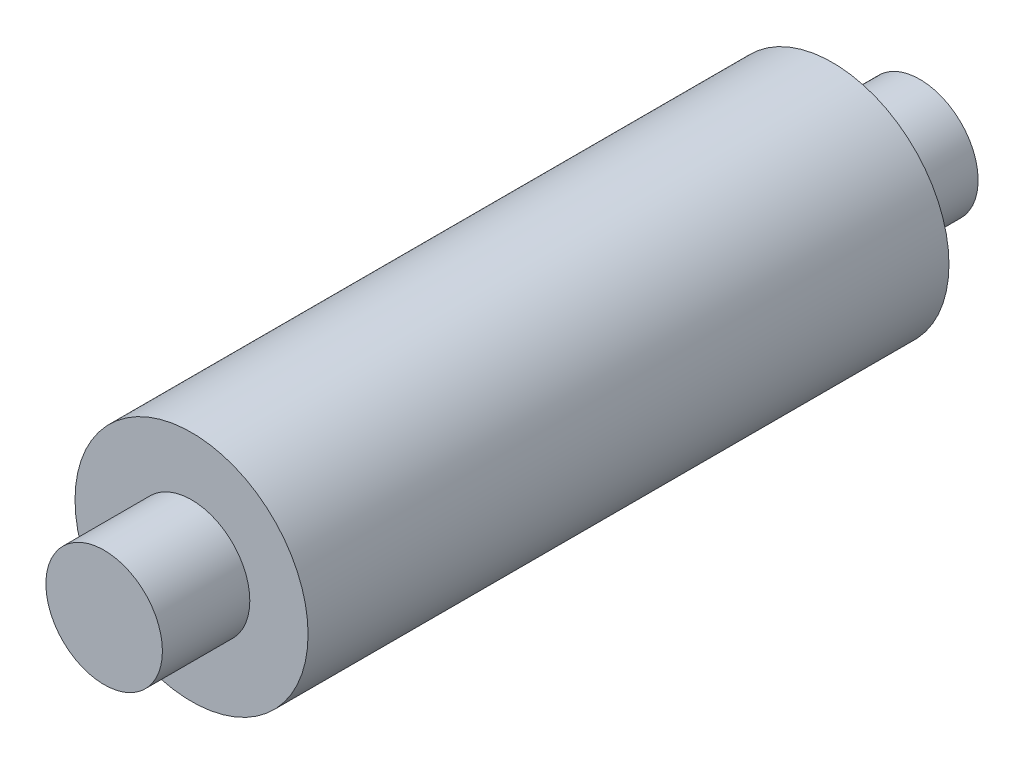
SolidWorks part; units mm, degrees
ref_plane "前视基准面" through (0, 0, 0) normal (0, 0, 1) x (1, 0, 0)
ref_plane "上视基准面" through (0, 0, 0) normal (0, 1, 0) x (1, 0, 0)
ref_plane "右视基准面" through (0, 0, 0) normal (1, 0, 0) x (0, 0, -1)
other "Configuration Table"
sketch "草图1" plane through (0, 0, 0) normal (0, 0, 1) x (1, 0, 0)
  circle A0 centre (0, 0) radius 2
  dimension "D1" = 4
extrude "凸台-拉伸1" add sketch "草图1" along normal blind 11
sketch "草图2" plane through (0, 0, 11) normal (0, 0, 1) x (1, 0, 0)
  circle A0 centre (0, 0) radius 1
  dimension "D1" = 2
extrude "凸台-拉伸2" add sketch "草图2" along normal blind 1.5
sketch "草图3" plane through (0, 0, 0) normal (0, 0, -1) x (-1, 0, 0)
  circle A0 centre (0, 0) radius 1
  dimension "D1" = 2
extrude "凸台-拉伸3" add sketch "草图3" along normal blind 1.5
